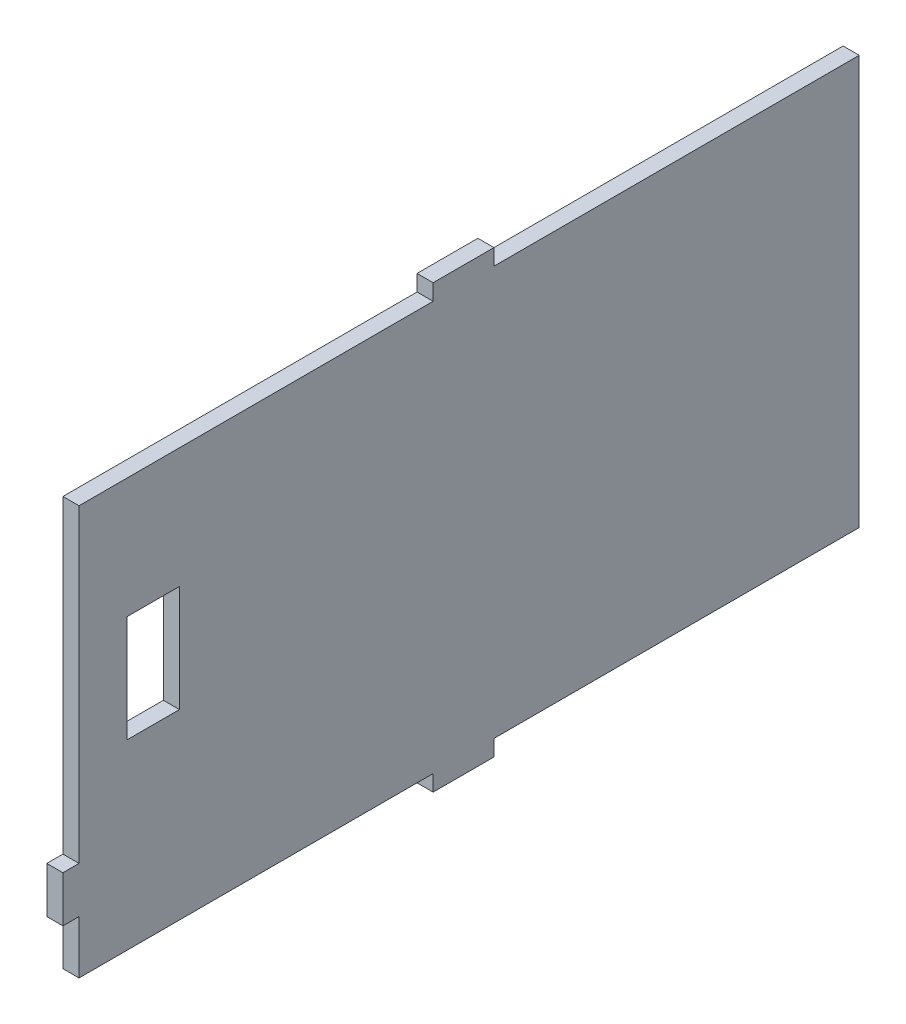
SolidWorks part; units mm, degrees
ref_plane "Front Plane" through (0, 0, 0) normal (0, 0, 1) x (1, 0, 0)
ref_plane "Top Plane" through (0, 0, 0) normal (0, 1, 0) x (1, 0, 0)
ref_plane "Right Plane" through (0, 0, 0) normal (1, 0, 0) x (0, 0, -1)
sketch "Sketch1" plane through (0, 0, 0) normal (1, 0, 0) x (0, 0, -1)
  line L1 (0, 0) -> (-38.1, 0)
  line L2 (0, 0) -> (0, 40.325)
  line L3 (0, 40.325) -> (-38.1, 40.325)
  line L4 (-38.1, 0) -> (-38.1, 40.325)
  dimension "D1" = 40.325
  dimension "D2" = 38.1
extrude "Boss-Extrude1" add sketch "Sketch1" along normal blind 3.175 contours L3 L4 L1 L2
sketch "Sketch3" plane through (3.175, 0, 0) normal (1, 0, 0) x (0, 0, -1)
  line L1 (-38.1, 40.325) -> (-34.925, 40.325)
  line L2 (-38.1, 40.325) -> (-38.1, 29.835)
  line L3 (-38.1, 29.835) -> (-34.925, 29.835)
  line L4 (-34.925, 40.325) -> (-34.925, 29.835)
  line L5 (-38.1, 0) -> (-34.925, 0)
  line L6 (-38.1, 0) -> (-38.1, 20.695)
  line L7 (-38.1, 20.695) -> (-34.925, 20.695)
  line L8 (-34.925, 0) -> (-34.925, 20.695)
  dimension "D1" = 3.175
  dimension "D2" = 3.175
  dimension "D3" = 9.14
  dimension "D4" = 10.49
extrude "Cut-Extrude2" cut sketch "Sketch3" against normal through all
sketch "Sketch4" plane through (3.175, 0, 0) normal (1, 0, 0) x (0, 0, -1)
  line L0 (-34.925, 0) -> (-21.025, 0) construction
  line L1 (0, 0) -> (-34.925, 0) construction
  line L2 (0, 0) -> (-12.2, 0) construction
  dimension "D1" = 13.9
  dimension "D2" = 12.2
sketch "Sketch5" plane through (0, 0, 0) normal (0, -1, 0) x (-1, 0, 0)
  line L0 (-3.175, -34.925) -> (-3.175, -21.025) construction
  line L1 (-3.175, -21.025) -> (0, -21.025)
  line L2 (-3.175, -21.025) -> (-3.175, -9.025)
  line L3 (-3.175, -9.025) -> (0, -9.025)
  line L4 (0, -21.025) -> (0, -9.025)
  line L5 (-3.175, 0) -> (-3.175, -34.925) construction
  line L6 (0, 0) -> (0, -34.925) construction
  dimension "D1" = 12
extrude "Boss-Extrude2" add sketch "Sketch5" along normal blind 3.175
mirror "Mirror1" about plane through (3.175, 40.325, 0) normal (0, -1, 0) of "Boss-Extrude2", "Cut-Extrude2", "Boss-Extrude1"
sketch "Sketch7" plane through (0, 0, 0) normal (0, 0, -1) x (-1, 0, 0)
  line L0 (-3.175, 80.65) -> (0, 80.65) construction
  line L1 (0, 80.65) -> (-3.175, 80.65)
  line L2 (0, 80.65) -> (0, 0)
  line L3 (0, 0) -> (-3.175, 0)
  line L4 (-3.175, 80.65) -> (-3.175, 0)
extrude "Boss-Extrude3" add sketch "Sketch7" along normal blind 63
sketch "Sketch8" plane through (0, 0, 34.925) normal (0, 0, 1) x (1, 0, 0)
  line L1 (3.175, 80.65) -> (0, 80.65)
  line L2 (3.175, 80.65) -> (3.175, 0)
  line L3 (3.175, 0) -> (0, 0)
  line L4 (0, 80.65) -> (0, 0)
extrude "Boss-Extrude4" add sketch "Sketch8" along a picked direction on the side of the normal blind 55.9294
sketch "Sketch9" plane through (0, 0, 90.8544) normal (0, 0, 1) x (1, 0, 0)
  line L0 (3.175, 0) -> (3.175, 10.49) construction
  line L1 (3.175, 0) -> (3.175, 80.65) construction
  line L2 (0, 80.65) -> (0, 0) construction
  line L3 (3.175, 10.49) -> (0, 10.49)
  line L4 (3.175, 10.49) -> (3.175, 19.5727)
  line L5 (3.175, 19.5727) -> (0, 19.5727)
  line L6 (0, 10.49) -> (0, 19.5727)
  dimension "D1" = 10.49
extrude "Boss-Extrude5" add sketch "Sketch9" along normal blind 3.18
sketch "Sketch10" plane through (3.175, 0, 0) normal (1, 0, 0) x (0, 0, -1)
  line L1 (-71.0409, 56.9724) -> (-81.3579, 56.9724)
  line L2 (-71.0409, 56.9724) -> (-71.0409, 35.936)
  line L3 (-71.0409, 35.936) -> (-81.3579, 35.936)
  line L4 (-81.3579, 56.9724) -> (-81.3579, 35.936)
extrude "Cut-Extrude3" cut sketch "Sketch10" against normal blind 3.18
